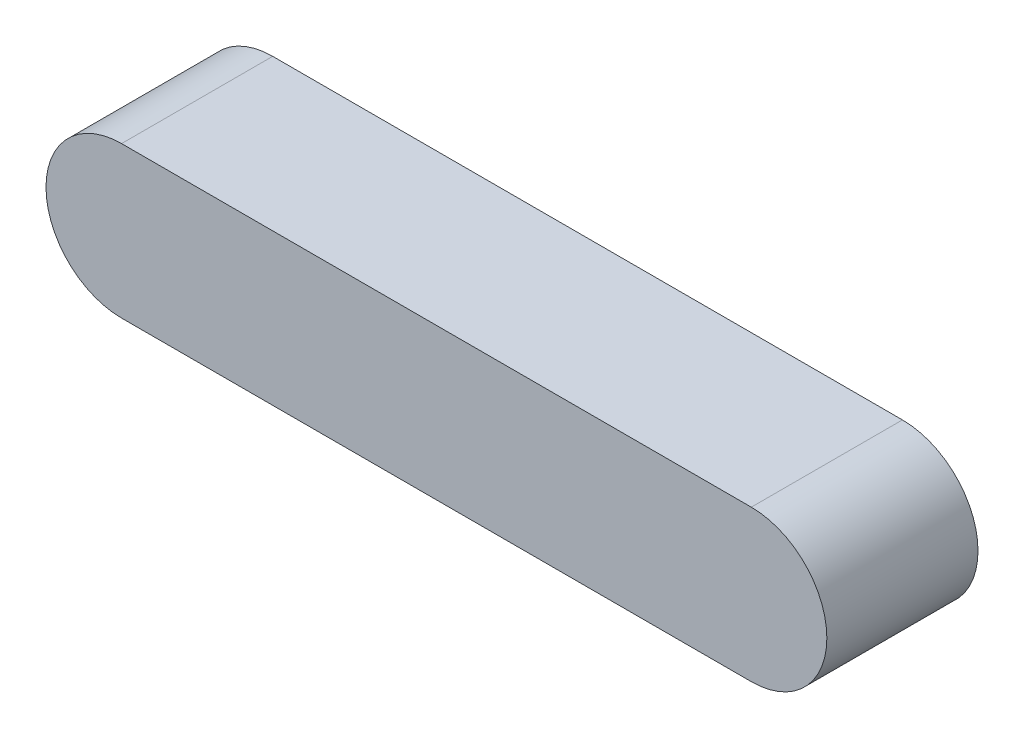
SolidWorks part; units mm, degrees
material "AISI 1020"
ref_plane "Спереди" through (0, 0, 0) normal (0, 0, 1) x (1, 0, 0)
ref_plane "Сверху" through (0, 0, 0) normal (0, 1, 0) x (1, 0, 0)
ref_plane "Справа" through (0, 0, 0) normal (1, 0, 0) x (0, 0, -1)
sketch "Эскиз1" plane through (0, 0, 0) normal (0, 0, 1) x (1, 0, 0)
  line L0 (-12.5, 3) -> (12.5, 3) construction
  line L1 (12.5, -3) -> (-12.5, -3) construction
  line L2 (-12.5, 3) -> (12.5, 3)
  line L3 (12.5, -3) -> (-12.5, -3)
  arc A0 (-12.5, 3) -> (-12.5, -3) centre (-12.5, 0) ccw construction
  arc A1 (12.5, -3) -> (12.5, 3) centre (12.5, 0) ccw construction
  arc A2 (-12.5, 3) -> (-12.5, -3) centre (-12.5, 0) ccw
  arc A3 (12.5, -3) -> (12.5, 3) centre (12.5, 0) ccw
extrude "Бобышка-Вытянуть1" add sketch "Эскиз1" against normal blind 6
